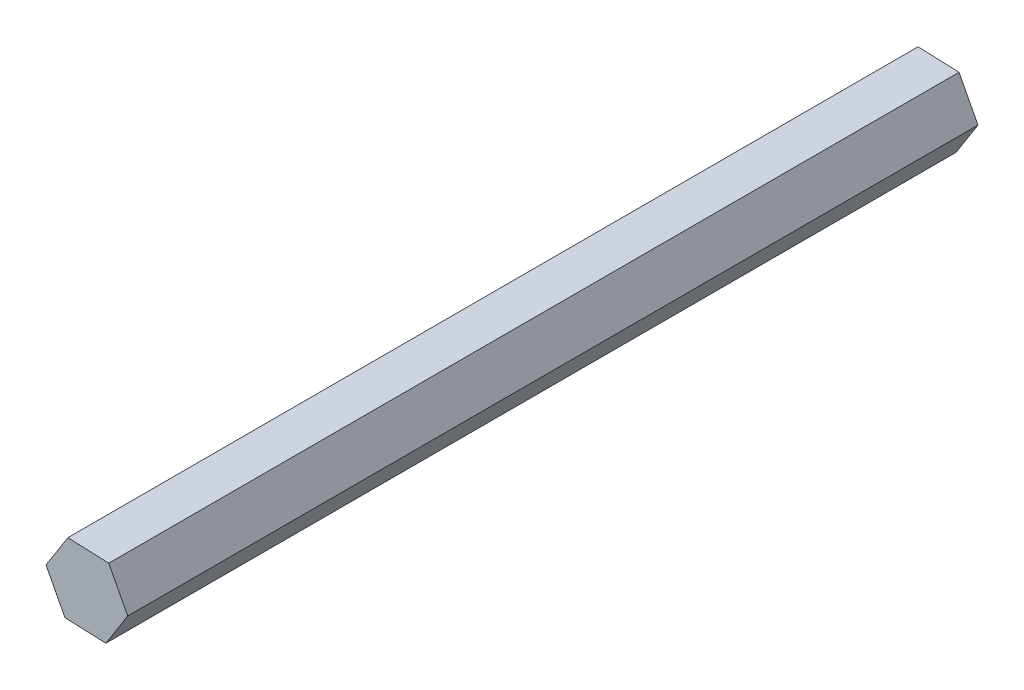
SolidWorks part; units mm, degrees
ref_plane "Front Plane" through (0, 0, 0) normal (0, 0, 1) x (1, 0, 0)
ref_plane "Top Plane" through (0, 0, 0) normal (0, 1, 0) x (1, 0, 0)
ref_plane "Right Plane" through (0, 0, 0) normal (1, 0, 0) x (0, 0, -1)
sketch "Sketch1" plane through (0, 0, 0) normal (0, 0, 1) x (1, 0, 0)
  line L1 (14.6523, -0.6017) -> (7.8472, 12.3885)
  line L2 (7.8472, 12.3885) -> (-6.8051, 12.9901)
  line L3 (-6.8051, 12.9901) -> (-14.6523, 0.6017)
  line L4 (-14.6523, 0.6017) -> (-7.8472, -12.3885)
  line L5 (-7.8472, -12.3885) -> (6.8051, -12.9901)
  line L6 (6.8051, -12.9901) -> (14.6523, -0.6017)
  circle A0 centre (0, 0) radius 12.7 construction
  dimension "D1" = 25.4
extrude "Boss-Extrude1" add sketch "Sketch1" along normal blind 304.8
